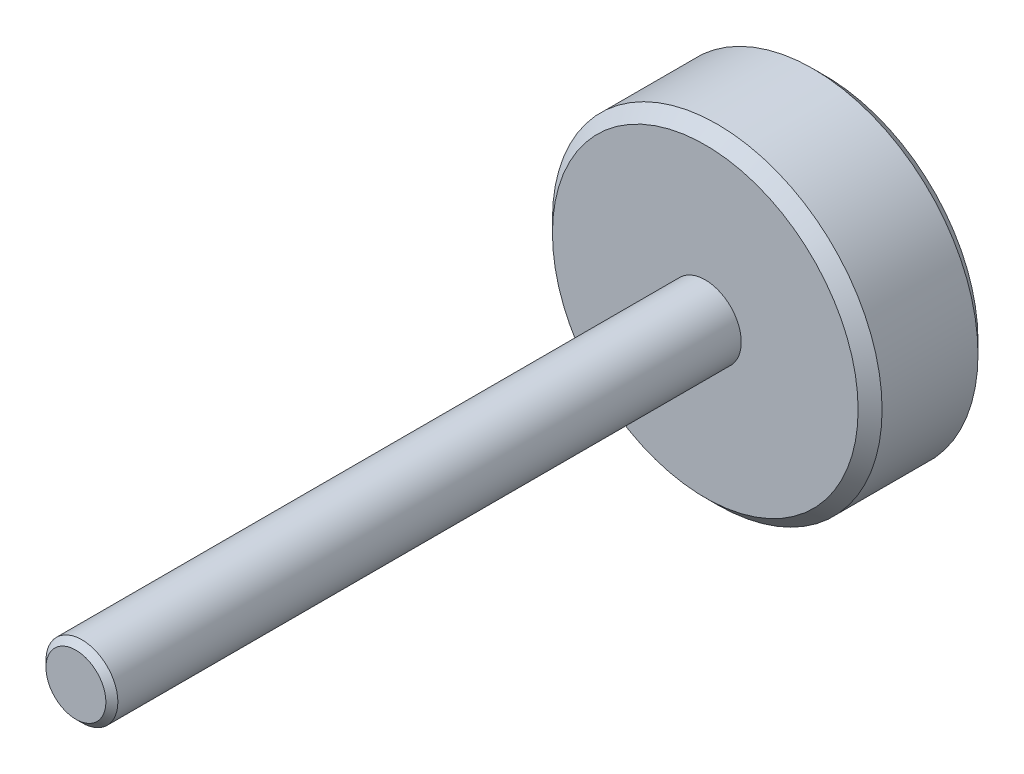
SolidWorks part; units mm, degrees
material "1.0037 (S235JR)"
ref_plane "Front Plane" through (0, 0, 0) normal (0, 0, 1) x (1, 0, 0)
ref_plane "Top Plane" through (0, 0, 0) normal (0, 1, 0) x (1, 0, 0)
ref_plane "Right Plane" through (0, 0, 0) normal (1, 0, 0) x (0, 0, -1)
sketch "Sketch1" plane through (0, 0, 0) normal (0, 0, 1) x (1, 0, 0)
  circle A0 centre (0, 0) radius 27.5
  dimension "D1" = 55
extrude "Boss-Extrude1" add sketch "Sketch1" along normal blind 20
sketch "Sketch2" plane through (0, 0, 20) normal (0, 0, 1) x (1, 0, 0)
  circle A0 centre (0, 0) radius 6
  dimension "D1" = 12
extrude "Boss-Extrude2" add sketch "Sketch2" along normal blind 105
chamfer "Chamfer1" distance 1 angle 45 1 edges at (6, 0, 125)
chamfer "Chamfer2" distance 2 angle 45 2 edges at (27.5, 0, 0) (27.5, 0, 20)
